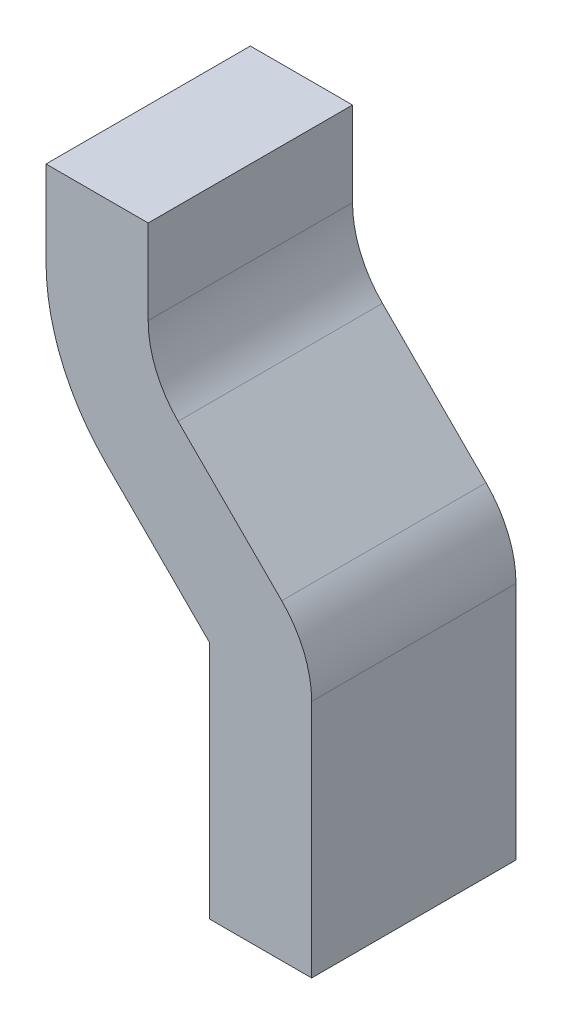
SolidWorks part; units mm, degrees
ref_plane "Plan de face" through (0, 0, 0) normal (0, 0, 1) x (1, 0, 0)
ref_plane "Plan de dessus" through (0, 0, 0) normal (0, 1, 0) x (1, 0, 0)
ref_plane "Plan de droite" through (0, 0, 0) normal (1, 0, 0) x (0, 0, -1)
sketch "Esquisse1" plane through (0, 0, 0) normal (0, 0, 1) x (1, 0, 0)
  line L0 (0, 0) -> (0, 1.1721)
  line L1 (0.5, 0) -> (0.5, 1.1721)
  line L2 (-0.89, 0) -> (2.6662, 0) construction
  line L3 (0.3536, 1.5256) -> (-0.1536, 2.0327)
  line L4 (-0.3, 2.8) -> (-0.3, 2.3863)
  line L5 (0, 1.1721) -> (-0.5071, 1.6792)
  line L6 (-0.8, 2.8) -> (-0.8, 2.3863)
  line L7 (0, 0) -> (0.5, 0)
  line L8 (-0.8, 2.8) -> (-0.3, 2.8)
  arc A0 (0.5, 1.1721) -> (0.3536, 1.5256) centre (0, 1.1721) ccw
  arc A1 (-0.1536, 2.0327) -> (-0.3, 2.3863) centre (0.2, 2.3863) cw
  arc A2 (-0.5071, 1.6792) -> (-0.8, 2.3863) centre (0.2, 2.3863) cw
extrude "Boss.-Extru.1" add sketch "Esquisse1" along normal blind 1
